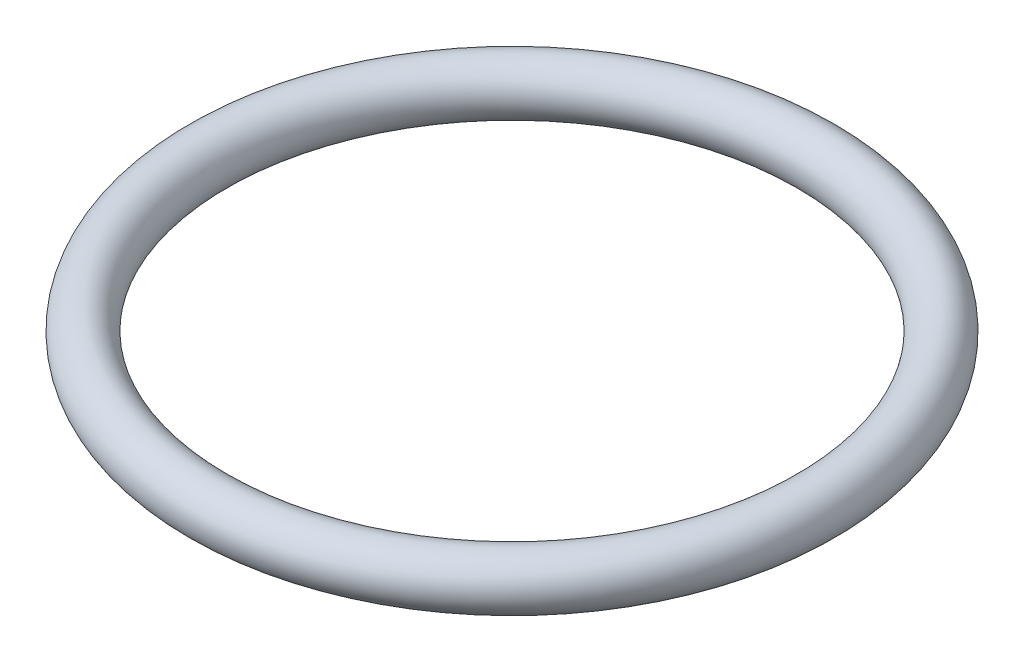
SolidWorks part; units mm, degrees
ref_plane "Front" through (0, 0, 0) normal (0, 0, 1) x (1, 0, 0)
ref_plane "Top" through (0, 0, 0) normal (0, 1, 0) x (1, 0, 0)
ref_plane "Right" through (0, 0, 0) normal (1, 0, 0) x (0, 0, -1)
sketch "Esquisse1" plane through (0, 0, 0) normal (0, 0, 1) x (1, 0, 0)
  line L0 (0, 0) -> (0, 13.481) construction
  line L1 (29, 0) -> (0, 0) construction
  circle A0 centre (29, 0) radius 2.5
  dimension "D2" = 5
  dimension "D1" = 29
revolve "Révolution1" add sketch "Esquisse1" angle 360 about L0
